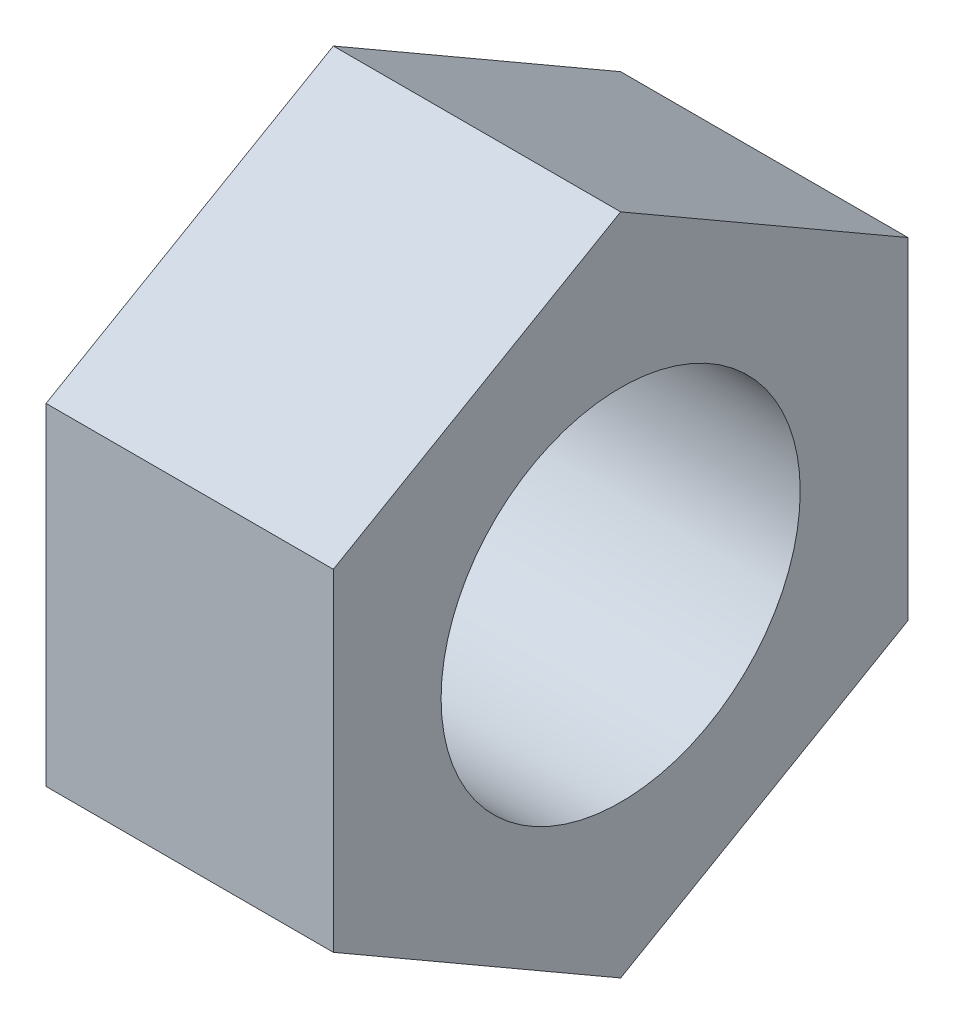
SolidWorks part; units mm, degrees
ref_plane "Front Plane" through (0, 0, 0) normal (0, 0, 1) x (1, 0, 0)
ref_plane "Top Plane" through (0, 0, 0) normal (0, 1, 0) x (1, 0, 0)
ref_plane "Right Plane" through (0, 0, 0) normal (1, 0, 0) x (0, 0, -1)
sketch "Sketch1" plane through (0, 0, 0) normal (1, 0, 0) x (0, 0, -1)
  line L1 (0, 7.3323) -> (-6.35, 3.6662)
  line L2 (-6.35, 3.6662) -> (-6.35, -3.6662)
  line L3 (-6.35, -3.6662) -> (0, -7.3323)
  line L4 (0, -7.3323) -> (6.35, -3.6662)
  line L5 (6.35, -3.6662) -> (6.35, 3.6662)
  line L6 (6.35, 3.6662) -> (0, 7.3323)
  circle A0 centre (0, 0) radius 6.35 construction
  circle A1 centre (0, 0) radius 3.9688
  dimension "D3" = 7.9375
  dimension "D1" = 6.35
  dimension "D2" = 3.6662
extrude "Boss-Extrude1" add sketch "Sketch1" along normal blind 6.35
